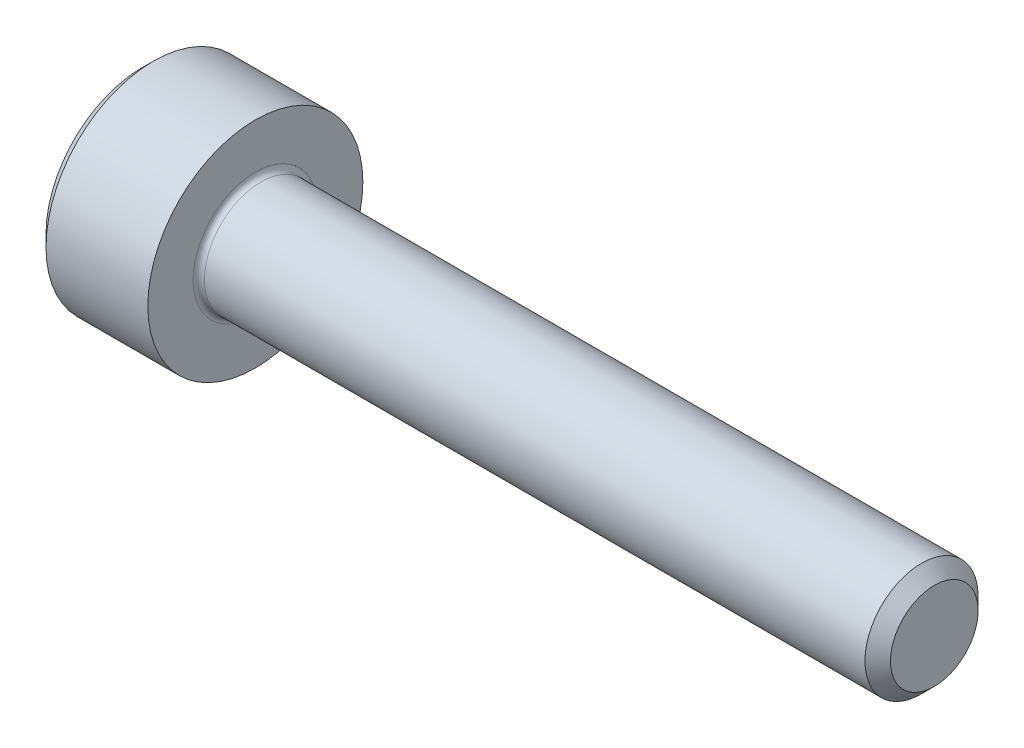
SolidWorks part; units mm, degrees
revolve "Base-Revolve" add sketch "BodySke"
sketch "BodySke" plane through (0, 0, 0) normal (0, 0, 1) x (1, 0, 0)
  line L0 (0, 0) -> (0, 1.7)
  line L1 (0.2, 1.9) -> (2, 1.9)
  line L2 (2, 1.9) -> (2, 1)
  line L3 (2, 1) -> (13.774, 1)
  line L4 (14, 0.774) -> (14, 0)
  line L5 (14, 0) -> (0, 0)
  line L6 (-31.75, 0) -> (127, 0) construction
  line L7 (0, 1.7) -> (0.2, 1.9)
  line L8 (14, 0.774) -> (13.774, 1)
  line L9 (0, -1.7) -> (0.2, -1.9) construction
  line L10 (14, -0.774) -> (13.774, -1) construction
  line L11 (2.4, 9.525) -> (2.4, 3.175) construction
  line L12 (2, 9.525) -> (2, 3.175) construction
  line L13 (-36, 9.525) -> (-36, 3.175) construction
  dimension "Diameter" = 2
  dimension "Head_ht" = 2
  dimension "Length" = 12
  dimension "Body_ch_ang" = 45
  dimension "Head_dia" = 3.8
  dimension "Head_ch_ang" = 45
  dimension "Minor_dia" = 1.548
  dimension "Advance" = 0.4
  dimension "Thread_nom" = 12
  dimension "Thread_length" = 50
  dimension "Head_ch_ht" = 0.2
cosmetic thread "ThreadCosmetic" [suppressed]
fillet "Fillet1" radius 0.1 1 edges at (2, 0, 1)
ref_plane "Plane1" through (0, 0, 0) normal (0, 0, 1) x (1, 0, 0)
ref_plane "Plane2" through (0, 0, 0) normal (0, 1, 0) x (1, 0, 0)
ref_plane "Plane3" through (0, 0, 0) normal (1, 0, 0) x (0, 0, -1)
sketch "Sketch2" plane through (0, 0, 0) normal (0, 0, 1) x (1, 0, 0)
  line L0 (0, 0.7725) -> (1, 0.7725)
  line L1 (1, 0.7725) -> (1.446, 0)
  line L2 (-31.75, 0) -> (127, 0) construction
  line L3 (1.446, 0) -> (0, 0)
  line L4 (0, 0) -> (0, 0.7725)
  line L5 (0, 1.7) -> (0, -1.7) construction
  line L6 (0, 0) -> (47.625, 0) construction
  line L7 (2, -1.9) -> (2, 1.9) construction
  dimension "D1" = 0.7725
  dimension "D2" = 60
revolve "Hex-PreBroach" cut sketch "Sketch2" angle 360 about L6
sketch "Sketch3" plane through (0, 0, 0) normal (-1, 0, 0) x (0, 0.5, 0.866)
  line L0 (0.446, 0.7725) -> (-0.446, 0.7725)
  line L1 (-0.446, 0.7725) -> (-0.892, 0)
  line L2 (0.446, 0.7725) -> (0.892, 0)
  line L3 (0.446, -0.7725) -> (0.892, 0)
  line L4 (0.446, -0.7725) -> (-0.446, -0.7725)
  line L5 (-0.446, -0.7725) -> (-0.892, 0)
  dimension "D1" = 0.7725
  dimension "D2" = 0.7725
  dimension "Hex_size" = 1.545
extrude "Hex" cut sketch "Sketch3" against normal blind 1
sketch "Sketch4" plane through (0, 0, 0) normal (-1, 0, 0) x (0, 0, 1)
  line L0 (0, 0) -> (0.9398, 0)
  line L1 (0, 0) -> (6.1484, 3.5498) construction
  line L2 (0, 0) -> (0.4699, 0.8139)
  line L3 (0.7832, 0.2175) -> (0.8962, 0.2828)
  line L4 (0.58, 0.5695) -> (0.693, 0.6348)
  arc A0 (0.7832, 0.2175) -> (0.58, 0.5695) centre (0, 0) ccw
  arc A1 (0.9398, 0) -> (0.8962, 0.2828) centre (0, 0) ccw
  arc A2 (0.4699, 0.8139) -> (0.693, 0.6348) centre (0, 0) cw
  dimension "D1" = 30
  dimension "D2" = 60
  dimension "Spline_p_dim" = 0.4064
  dimension "D3" = 0.2032
extrude "Spline" [suppressed] cut sketch "Sketch4" against normal blind 1
pattern_circular "CirPattern1" [suppressed] count 6 every 60
sketch "Sketch5" plane through (0, 0, 0) normal (0, 0, 1) x (1, 0, 0)
  line L0 (-31.75, 0) -> (127, 0) construction
  line L2 (0, 1.7) -> (0, -1.7) construction
  circle A0 centre (0.1, 0) radius 0.005
  dimension "Drilled_hole_dia" = 0.01
  dimension "Drilled_hole_loc" = 0.1
extrude "Hole" [suppressed] cut sketch "Sketch5" against normal through all and the other way through all
pattern_circular "Drilled-4" [suppressed] count 2 every 60
pattern_circular "Drilled-6" [suppressed] count 3 every 60
sketch "ThdSchSke" plane through (0, 0, 0) normal (0, 0, 1) x (1, 0, 0)
  line L0 (2.4, -0.774) -> (2.2418, -1)
  line L1 (2.4, -0.774) -> (2.5582, -1)
  line L2 (2.5582, -1) -> (2.5582, -1.25)
  line L3 (-3.175, 0) -> (5.1513, 0) construction
  line L5 (2.5582, -1.25) -> (2.2418, -1.25)
  line L6 (2.2418, -1.25) -> (2.2418, -1)
  line L7 (0, 1.7) -> (0, -1.7) construction
  dimension "Thread_minor" = 1.548
  dimension "Diameter" = 2
  dimension "Start" = 2.4
revolve "ThreadSchematic" [suppressed] cut sketch "ThdSchSke" angle 360 about L3
pattern_linear "ThdSchPat" [suppressed]
equation "\"D2@Sketch3\" = \"Hex_size@Sketch3\" / 2"
equation "\"D1@Sketch3\" = \"Hex_size@Sketch3\" / 2"
equation "\"D1@Sketch2\" = \"Hex_size@Sketch3\" / 2"
equation "\"D3@Sketch4\" = \"Spline_p_dim@Sketch4\" / 2"
equation "\"Thread_minor@ThreadCosmetic\"  =  \"Minor_dia@BodySke\""
equation "\"D2@CirPattern1\" = 360 / \"Num_teeth@CirPattern1\""
equation "\"Wall_thickness@Sketch2\" = \"Head_ht@BodySke\" - \"Key_eng@Hex\""
equation "\"Thread_length@ThreadCosmetic\" = ((sgn( (\"Length@BodySke\" - \"Advance@BodySke\" ) - \"Thread_nom@BodySke\" )-1)*( (\"Length@BodySke\" - \"Advance@BodySke\" ) - \"Thread_nom@BodySke\" ))/-2+ \"Thread_nom@BodySke\""
equation "\"Thread_minor@ThdSchSke\" = \"Minor_dia@BodySke\""
equation "\"Diameter@ThdSchSke\" = \"Diameter@BodySke\""
equation "\"Overcut@ThdSchSke\" = \"Diameter@BodySke\" * 1.25"
equation "\"Start@ThdSchSke\" = \"Head_ht@BodySke\" + \"Length@BodySke\" - \"Thread_length@ThreadCosmetic\"  '---Non-countersunk---"
equation "\"Num_threads@ThdSchPat\" = int( \"Thread_length@ThreadCosmetic\" / \"Advance@BodySke\" + 0.999 )  + 1"
equation "\"Advance@ThdSchPat\" = \"Thread_length@ThreadCosmetic\" /  (\"Num_threads@ThdSchPat\" - 1) 'relax it"
equation "\"Num_threads@ThdSchPat\" = \"Num_threads@ThdSchPat\" - sgn( \"Num_threads@ThdSchPat\" - 1) '---chamfered tips only---"
